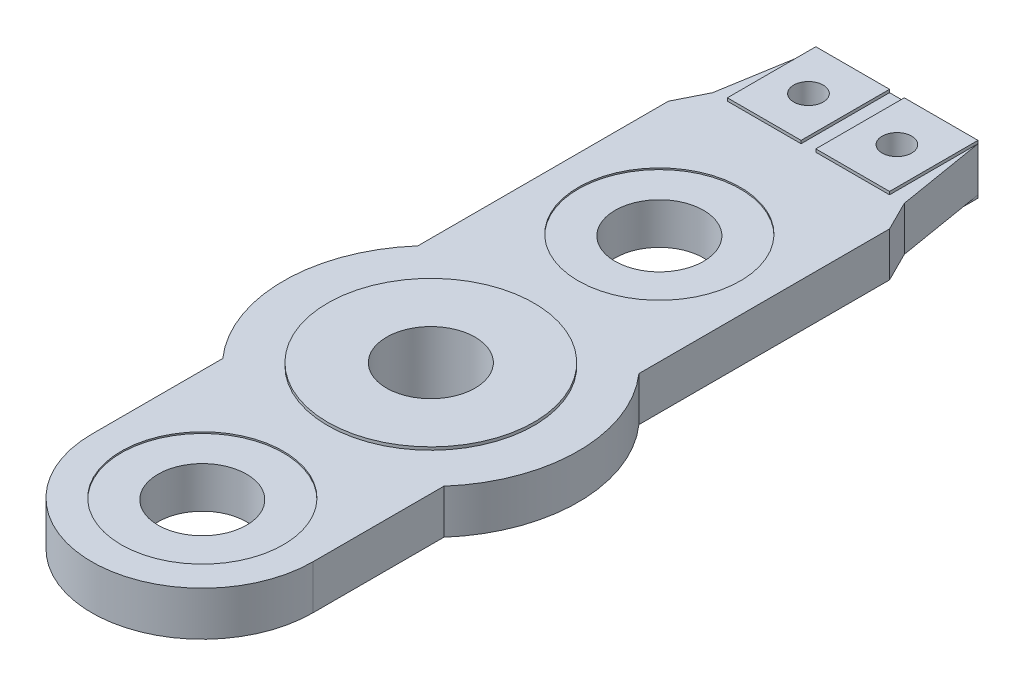
SolidWorks part; units mm, degrees
ref_plane "Front Plane" through (0, 0, 0) normal (0, 0, 1) x (1, 0, 0)
ref_plane "Top Plane" through (0, 0, 0) normal (0, 1, 0) x (1, 0, 0)
ref_plane "Right Plane" through (0, 0, 0) normal (1, 0, 0) x (0, 0, -1)
sketch "Sketch1" plane through (0, 0, 0) normal (0, 1, 0) x (1, 0, 0)
  line L0 (0, 7.75) -> (0, -7.75) construction
  line L1 (-3.75, -7.75) -> (-3.75, -3.3072)
  line L2 (3.75, -7.75) -> (3.75, -3.3072)
  line L3 (3.75, 3.3072) -> (3.75, 11.8072)
  line L4 (-3.75, 3.3072) -> (-3.75, 11.8072)
  line L5 (-3.75, 11.8072) -> (-3.25, 12.8072)
  line L6 (-3.25, 12.8072) -> (-2.75, 15.8072)
  line L7 (-2.75, 15.8072) -> (2.75, 15.8072)
  line L8 (2.75, 15.8072) -> (3.25, 12.8072)
  line L9 (3.25, 12.8072) -> (3.75, 11.8072)
  line L10 (-1.5, 14.3072) -> (1.5, 14.3072) construction
  arc A0 (-3.75, 3.3072) -> (-3.75, -3.3072) centre (0, 0) ccw
  circle A1 centre (0, -7.75) radius 1.5
  arc A2 (-3.75, -7.75) -> (3.75, -7.75) centre (0, -7.75) ccw
  circle A3 centre (0, 7.75) radius 1.5
  circle A4 centre (0, 7.75) radius 3.75 construction
  arc A5 (-2.0044, 4.5806) -> (-3.75, 3.3072) centre (0, 0) ccw construction
  arc A6 (0, 5) -> (-2.0044, 4.5806) centre (0, 0) ccw construction
  arc A7 (3.75, 3.3072) -> (2.0044, 4.5806) centre (0, 0) ccw construction
  arc A8 (2.0044, 4.5806) -> (0, 5) centre (0, 0) ccw construction
  arc A9 (2.0044, -4.5806) -> (3.75, -3.3072) centre (0, 0) ccw construction
  arc A10 (3.75, -3.3072) -> (3.75, 3.3072) centre (0, 0) ccw
  arc A11 (2.0044, -4.5806) -> (0, -4) centre (0, -7.75) ccw construction
  arc A12 (0, -5) -> (2.0044, -4.5806) centre (0, 0) ccw construction
  arc A13 (3.75, -7.75) -> (2.0044, -4.5806) centre (0, -7.75) ccw construction
  arc A14 (0, -4) -> (-2.0044, -4.5806) centre (0, -7.75) ccw construction
  arc A15 (-2.0044, -4.5806) -> (0, -5) centre (0, 0) ccw construction
  arc A16 (-2.0044, -4.5806) -> (-3.75, -7.75) centre (0, -7.75) ccw construction
  arc A17 (-3.75, -3.3072) -> (-2.0044, -4.5806) centre (0, 0) ccw construction
  circle A18 centre (-1.5, 14.3072) radius 0.5
  circle A19 centre (1.5, 14.3072) radius 0.5
  circle A20 centre (0, 0) radius 1.5
  point P10 (0, 0)
  point P24 (0, 15.8072)
  point P33 (0, 14.3072)
  point P34 (-3, 14.3072)
  dimension "D1" = 3
  dimension "D2" = 7.5
  dimension "D4" = 10
  dimension "D12" = 1
  dimension "D13" = 3
  dimension "D3" = 15.5
  dimension "D5" = 8.5
  dimension "D6" = 0.5
  dimension "D7" = 1
  dimension "D8" = 0.5
  dimension "D9" = 4
  dimension "D10" = 1
  dimension "D11" = 3
extrude "Boss-Extrude1" add sketch "Sketch1" along normal blind 1.5
sketch "Sketch2" plane through (0, 1.5, 0) normal (0, 1, 0) x (1, 0, 0)
  circle A0 centre (0, 0) radius 3.5
  arc A1 (3.75, -3.3072) -> (3.75, 3.3072) centre (0, 0) ccw construction
  circle A2 centre (0, 0) radius 1.5 construction
  circle A3 centre (0, 0) radius 1.5
  dimension "D1" = 1.5
extrude "Boss-Extrude2" add sketch "Sketch2" along normal blind 0.1
sketch "Sketch3" plane through (0, 1.5, 0) normal (0, 1, 0) x (1, 0, 0)
  circle A2 centre (0, -7.75) radius 2.75
  circle A3 centre (0, -7.75) radius 2.75
  circle A7 centre (0, 7.75) radius 2.75
  circle A8 centre (0, 7.75) radius 2.75
  dimension "D1" = 1.25
  dimension "D2" = 1.25
extrude "Cut-Extrude1" cut sketch "Sketch3" against normal blind 0.05
sketch "Sketch4" plane through (0, 0, 0) normal (0, -1, 0) x (1, 0, 0)
  circle A0 centre (0, -7.75) radius 2.75 construction
  circle A1 centre (0, 7.75) radius 2.75 construction
  circle A2 centre (0, -7.75) radius 2.75
  circle A3 centre (0, 7.75) radius 2.75
extrude "Cut-Extrude2" cut sketch "Sketch4" against normal blind 0.05
sketch "Sketch5" plane through (0, 0, 0) normal (0, -1, 0) x (1, 0, 0)
  circle A0 centre (0, 0) radius 2.75
  circle A1 centre (0, 0) radius 1.5 construction
  circle A2 centre (0, 0) radius 1.5
  dimension "D1" = 5.5
extrude "Boss-Extrude3" add sketch "Sketch5" along normal blind 1.5
fillet "Fillet1" radius 0.5 1 edges at (0, 0, 2.75)
sketch "Sketch6" plane through (0, 1.5, 0) normal (0, 1, 0) x (1, 0, 0)
  line L1 (-2.75, 15.8072) -> (-0.25, 15.8072)
  line L2 (-2.75, 15.8072) -> (-2.75, 12.8072)
  line L3 (-2.75, 12.8072) -> (-0.25, 12.8072)
  line L4 (-0.25, 15.8072) -> (-0.25, 12.8072)
  line L5 (-2.75, 15.8072) -> (-0.25, 12.8072) construction
  line L6 (-2.75, 12.8072) -> (-0.25, 15.8072) construction
  line L7 (2.75, 15.8072) -> (0.25, 15.8072)
  line L8 (2.75, 15.8072) -> (2.75, 12.8072)
  line L9 (2.75, 12.8072) -> (0.25, 12.8072)
  line L10 (0.25, 15.8072) -> (0.25, 12.8072)
  line L11 (2.75, 15.8072) -> (0.25, 12.8072) construction
  line L12 (2.75, 12.8072) -> (0.25, 15.8072) construction
  circle A0 centre (1.5, 14.3072) radius 0.5 construction
  circle A1 centre (-1.5, 14.3072) radius 0.5 construction
  circle A2 centre (1.5, 14.3072) radius 0.5
  circle A3 centre (-1.5, 14.3072) radius 0.5
  point P10 (-1.5, 14.3072)
  point P16 (1.5, 14.3072)
extrude "Boss-Extrude4" add sketch "Sketch6" along normal blind 0.1
sketch "Sketch7" plane through (0, 0, 0) normal (0, -1, 0) x (1, 0, 0)
  line L0 (-2.75, -15.8072) -> (-2.75, -12.8072) construction
  line L1 (-2.75, -12.8072) -> (-0.25, -12.8072) construction
  line L2 (-0.25, -12.8072) -> (-0.25, -15.8072) construction
  line L3 (-0.25, -15.8072) -> (-2.75, -15.8072) construction
  line L4 (2.75, -12.8072) -> (2.75, -15.8072) construction
  line L5 (2.75, -15.8072) -> (0.25, -15.8072) construction
  line L6 (0.25, -15.8072) -> (0.25, -12.8072) construction
  line L7 (0.25, -12.8072) -> (2.75, -12.8072) construction
  line L8 (-2.75, -15.8072) -> (-2.75, -12.8072)
  line L9 (-2.75, -12.8072) -> (-0.25, -12.8072)
  line L10 (-0.25, -12.8072) -> (-0.25, -15.8072)
  line L11 (-0.25, -15.8072) -> (-2.75, -15.8072)
  line L12 (2.75, -12.8072) -> (2.75, -15.8072)
  line L13 (2.75, -15.8072) -> (0.25, -15.8072)
  line L14 (0.25, -15.8072) -> (0.25, -12.8072)
  line L15 (0.25, -12.8072) -> (2.75, -12.8072)
  circle A0 centre (-1.5, -14.3072) radius 0.5 construction
  circle A1 centre (1.5, -14.3072) radius 0.5 construction
  circle A2 centre (-1.5, -14.3072) radius 0.5
  circle A3 centre (1.5, -14.3072) radius 0.5
extrude "Boss-Extrude5" add sketch "Sketch7" along normal blind 0.1
